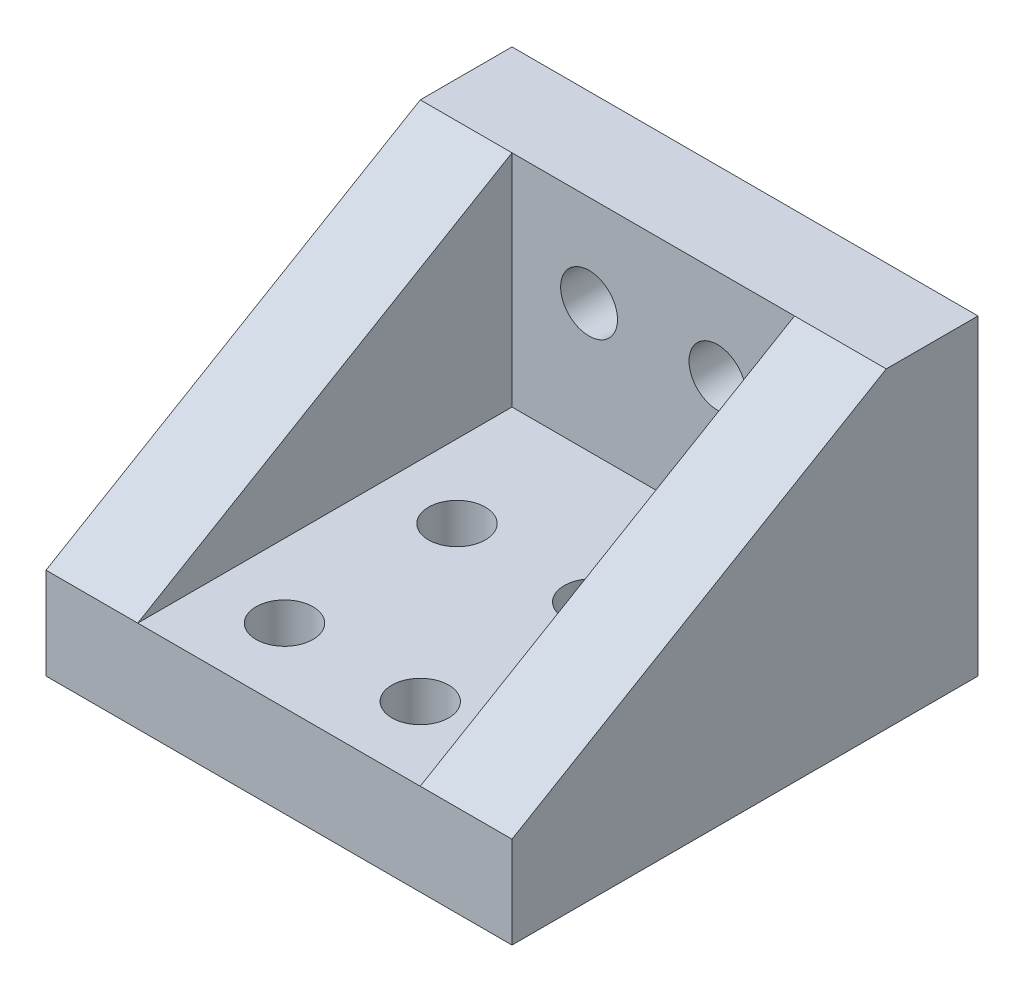
SolidWorks part; units mm, degrees
material "6061-T6 (SS)"
ref_plane "Front Plane" through (0, 0, 0) normal (0, 0, 1) x (1, 0, 0)
ref_plane "Top Plane" through (0, 0, 0) normal (0, 1, 0) x (1, 0, 0)
ref_plane "Right Plane" through (0, 0, 0) normal (1, 0, 0) x (0, 0, -1)
sketch "Sketch3" plane through (0, 0, 0) normal (1, 0, 0) x (0, 0, -1)
  line L0 (0, 0) -> (0, 5)
  line L1 (0, 5) -> (20.4, 5)
  line L2 (20.4, 5) -> (20.4, 17)
  line L3 (20.4, 17) -> (25.4, 17)
  line L4 (25.4, 17) -> (25.4, 0)
  line L5 (25.4, 0) -> (0, 0)
  dimension "D1" = 17
  dimension "D2" = 5
  dimension "D3" = 25.4
extrude "Boss-Extrude2" add sketch "Sketch3" along normal blind 25.4
sketch "Sketch4" plane through (0, 0, -25.4) normal (0, 0, -1) x (-1, 0, 0)
  line L0 (-16.2, 12) -> (-9.2, 12) construction
  line L2 (-12.7, 12) -> (-12.7, 17) construction
  line L3 (-25.4, 17) -> (0, 17) construction
  circle A0 centre (-16.2, 12) radius 1.55
  circle A1 centre (-9.2, 12) radius 1.55
  dimension "D2" = 3.1
  dimension "D1" = 7
  dimension "D3" = 5
extrude "Cut-Extrude1" cut sketch "Sketch4" against normal up to next
sketch "Sketch8" plane through (0, 0, 0) normal (-1, 0, 0) x (0, 0, 1)
  line L0 (-20.4, 17) -> (0, 5)
rib "Rib12" sketch "Sketch8" sketch "Sketch8" thickness 5 extrusion direction parallel to sketch draft on no parameters "D1"=5
ref_plane "Plane4" through (12.7, 0, 0) normal (1, 0, 0) x (0, 0, -1)
mirror "Mirror1" about plane through (12.7, 0, 0) normal (1, 0, 0) of "Rib12"
sketch "Sketch5" plane through (0, 5, 0) normal (0, 1, 0) x (1, 0, 0)
  line L1 (9, 4) -> (16.4, 4) construction
  line L2 (9, 4) -> (9, 13.4) construction
  line L3 (9, 13.4) -> (16.4, 13.4) construction
  line L4 (16.4, 4) -> (16.4, 13.4) construction
  line L10 (9, 13.4) -> (5, 13.4) construction
  line L13 (5, 20.4) -> (5, 0) construction
  line L14 (9, 13.4) -> (9, 20.4) construction
  line L15 (20.4, 20.4) -> (5, 20.4) construction
  line L16 (16.4, 4) -> (16.4, 0) construction
  line L17 (20.4, 0) -> (5, 0) construction
  line L18 (16.4, 4) -> (20.4, 4) construction
  line L19 (20.4, 20.4) -> (20.4, 0) construction
  circle A0 centre (9, 4) radius 1.55
  circle A1 centre (9, 13.4) radius 1.55
  circle A2 centre (16.4, 13.4) radius 1.55
  circle A3 centre (16.4, 4) radius 1.55
  dimension "D2" = 3.1
  dimension "D1" = 4
  dimension "D3" = 7
  dimension "D4" = 4
extrude "Cut-Extrude2" cut sketch "Sketch5" against normal up to next
